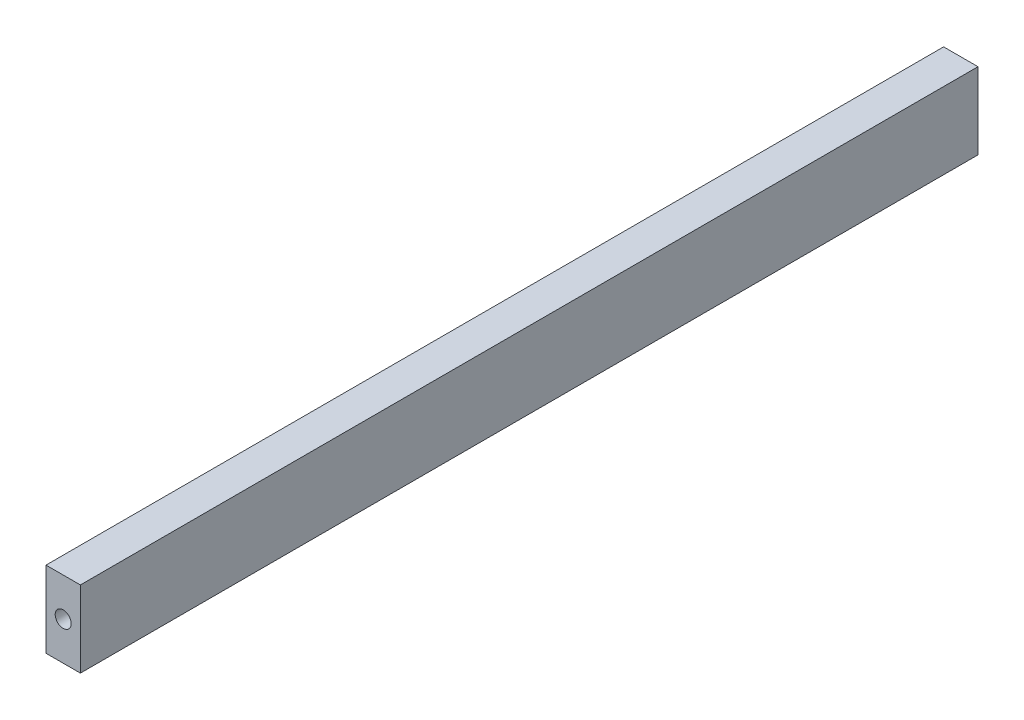
SolidWorks part; units mm, degrees
ref_plane "Front Plane" through (0, 0, 0) normal (0, 0, 1) x (1, 0, 0)
ref_plane "Top Plane" through (0, 0, 0) normal (0, 1, 0) x (1, 0, 0)
ref_plane "Right Plane" through (0, 0, 0) normal (1, 0, 0) x (0, 0, -1)
sketch "Sketch1" plane through (0, 0, 0) normal (0, 0, 1) x (1, 0, 0)
  line L1 (-4.5, -10) -> (4.5, -10)
  line L2 (-4.5, -10) -> (-4.5, 10)
  line L3 (-4.5, 10) -> (4.5, 10)
  line L4 (4.5, -10) -> (4.5, 10)
  line L5 (-4.5, -10) -> (4.5, 10) construction
  line L6 (-4.5, 10) -> (4.5, -10) construction
  point P0 (0, 0)
  dimension "D1" = 20
  dimension "D2" = 9
extrude "Boss-Extrude1" add sketch "Sketch1" along normal mid plane 235
sketch "Sketch2" plane through (0, 0, 117.5) normal (0, 0, 1) x (1, 0, 0)
  circle A0 centre (0, 0) radius 2.1
  dimension "D1" = 4.2
extrude "Cut-Extrude1" cut sketch "Sketch2" against normal blind 11
mirror "Mirror1" about plane through (0, 0, 0) normal (0, 0, 1) of "Cut-Extrude1"
